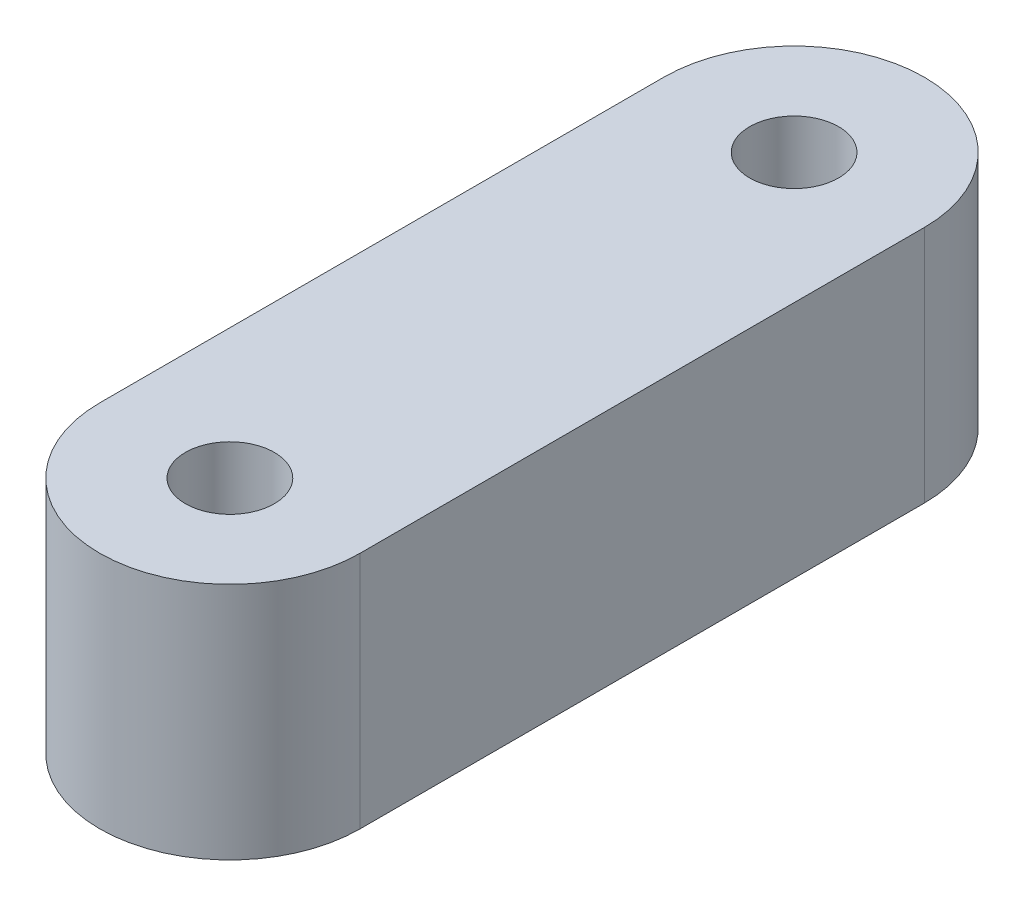
SolidWorks part; units mm, degrees
ref_plane "前视基准面" through (0, 0, 0) normal (0, 0, 1) x (1, 0, 0)
ref_plane "上视基准面" through (0, 0, 0) normal (0, 1, 0) x (1, 0, 0)
ref_plane "右视基准面" through (0, 0, 0) normal (1, 0, 0) x (0, 0, -1)
sketch "草图1" plane through (0, 0, 0) normal (0, 1, 0) x (1, 0, 0)
  line L0 (0, -13) -> (0, 13) construction
  line L1 (-6, -13) -> (-6, 13)
  line L2 (6, -13) -> (6, 13)
  arc A0 (-6, -13) -> (6, -13) centre (0, -13) ccw
  arc A1 (6, 13) -> (-6, 13) centre (0, 13) ccw
  point P2 (0, 0)
  dimension "D1" = 26
  dimension "D2" = 12
extrude "凸台-拉伸1" add sketch "草图1" along normal blind 11
sketch "草图2" plane through (0, 11, 0) normal (0, 1, 0) x (1, 0, 0)
  circle A0 centre (0, 13) radius 2.05
  circle A1 centre (0, -13) radius 2.05
  dimension "D1" = 13
  dimension "D3" = 4.1
  dimension "D4" = 4.1
  dimension "D5" = 0
  dimension "D6" = 0
  dimension "D2" = 13
extrude "切除-拉伸1" cut sketch "草图2" against normal through all
sketch "草图3" plane through (-6, 0, 0) normal (-1, 0, 0) x (0, 0, 1)
  line L0 (-13, 0) -> (13, 0) construction
  circle A0 centre (0, 5.5) radius 3.1
  dimension "D1" = 5.5
  dimension "D2" = 6.2
extrude "切除-拉伸2" cut sketch "草图3" against normal blind 10
